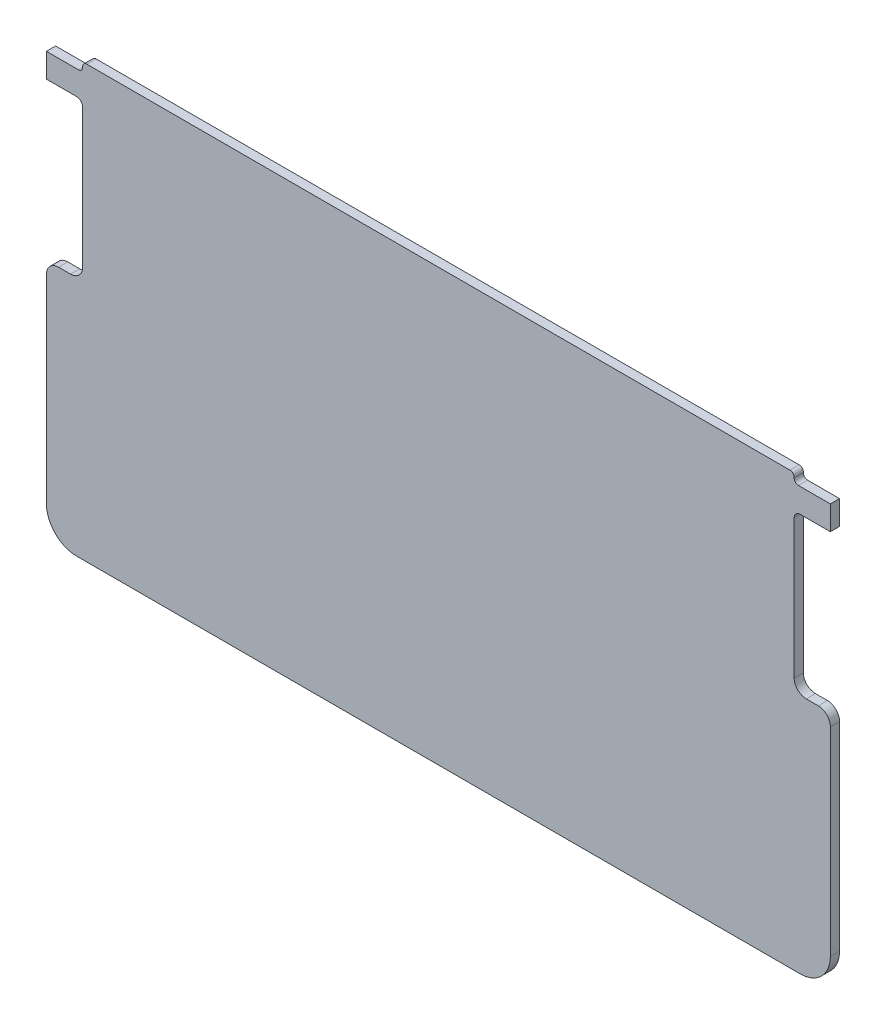
SolidWorks part; units mm, degrees
ref_plane "Front Plane" through (0, 0, 0) normal (0, 0, 1) x (1, 0, 0)
ref_plane "Top Plane" through (0, 0, 0) normal (0, 1, 0) x (1, 0, 0)
ref_plane "Right Plane" through (0, 0, 0) normal (1, 0, 0) x (0, 0, -1)
sketch "Sketch1" plane through (0, 0, 0) normal (0, 0, 1) x (1, 0, 0)
  line L0 (-29.5, -34) -> (-29.5, -1.5) construction
  line L1 (-29.5, 1) -> (29.5, 1) construction
  line L2 (-29.5, 1) -> (-29.5, -34) construction
  line L3 (-29.5, -34) -> (29.5, -34)
  line L4 (29.5, 1) -> (29.5, -34) construction
  line L5 (-29.5, 1) -> (29.5, -34) construction
  line L6 (-29.5, -34) -> (29.5, 1) construction
  line L7 (-30, -1) -> (-32.5, -1)
  line L8 (-32.5, -1) -> (-32.5, 1)
  line L9 (-32.5, 1) -> (32.5, 1) construction
  line L10 (29.5, -34) -> (29.5, -1.5) construction
  line L11 (30, -1) -> (32.5, -1)
  line L12 (32.5, -1) -> (32.5, 1)
  line L13 (-29.5, -1.5) -> (-29.5, -13)
  line L14 (-30.5, -14) -> (-31.5, -14)
  line L15 (-32.5, -15) -> (-32.5, -31.5)
  line L16 (-30, -34) -> (-29.5, -34)
  line L17 (29.5, -34) -> (30, -34)
  line L18 (32.5, -31.5) -> (32.5, -15)
  line L19 (31.5, -14) -> (30.5, -14)
  line L20 (29.5, -13) -> (29.5, -1.5)
  line L21 (-39.6398, 0) -> (38.7891, 0) construction
  line L22 (-32.5, 1) -> (-29.85, 1)
  line L23 (-29.5, 1.35) -> (-29.5, 1.4)
  line L24 (-29.15, 1.75) -> (29.15, 1.75)
  line L25 (29.5, 1.4) -> (29.5, 1.35)
  line L26 (29.85, 1) -> (32.5, 1)
  arc A0 (30, -1) -> (29.5, -1.5) centre (30, -1.5) ccw
  arc A1 (-29.5, -1.5) -> (-30, -1) centre (-30, -1.5) ccw
  arc A2 (32.5, -15) -> (31.5, -14) centre (31.5, -15) ccw
  arc A3 (-31.5, -14) -> (-32.5, -15) centre (-31.5, -15) ccw
  arc A4 (30.5, -14) -> (29.5, -13) centre (30.5, -13) cw
  arc A5 (-29.5, -13) -> (-30.5, -14) centre (-30.5, -13) cw
  arc A6 (32.5, -31.5) -> (30, -34) centre (30, -31.5) cw
  arc A7 (-30, -34) -> (-32.5, -31.5) centre (-30, -31.5) cw
  arc A8 (29.15, 1.75) -> (29.5, 1.4) centre (29.15, 1.4) cw
  arc A9 (-29.5, 1.4) -> (-29.15, 1.75) centre (-29.15, 1.4) cw
  arc A10 (29.5, 1.35) -> (29.85, 1) centre (29.85, 1.35) ccw
  arc A11 (-29.85, 1) -> (-29.5, 1.35) centre (-29.85, 1.35) ccw
  point P0 (0, -16.5)
  point P14 (29.5, -1)
  point P17 (-29.5, -1)
  point P19 (-32.5, 0)
  point P34 (29.5, -14)
  point P37 (-29.5, -14)
  point P41 (-32.5, -34)
  dimension "D5" = 0.5
  dimension "D8" = 1
  dimension "D9" = 1
  dimension "D10" = 1
  dimension "D11" = 1
  dimension "D7" = 2.5
  dimension "D12" = 2.5
  dimension "D15" = 0.35
  dimension "D1" = 35
  dimension "D2" = 59
  dimension "D3" = 2
  dimension "D4" = 3
  dimension "D6" = 3
  dimension "D13" = 14
  dimension "D14" = 0.75
extrude "Boss-Extrude1" add sketch "Sketch1" along normal blind 0.381 and the other way blind 0.381
sketch "Sketch2" plane through (0, 0, 0) normal (0, 0, 1) x (1, 0, 0)
  line L0 (-40, 0) -> (40, 0) construction
  point P4 (0, 0)
  dimension "D1" = 80
